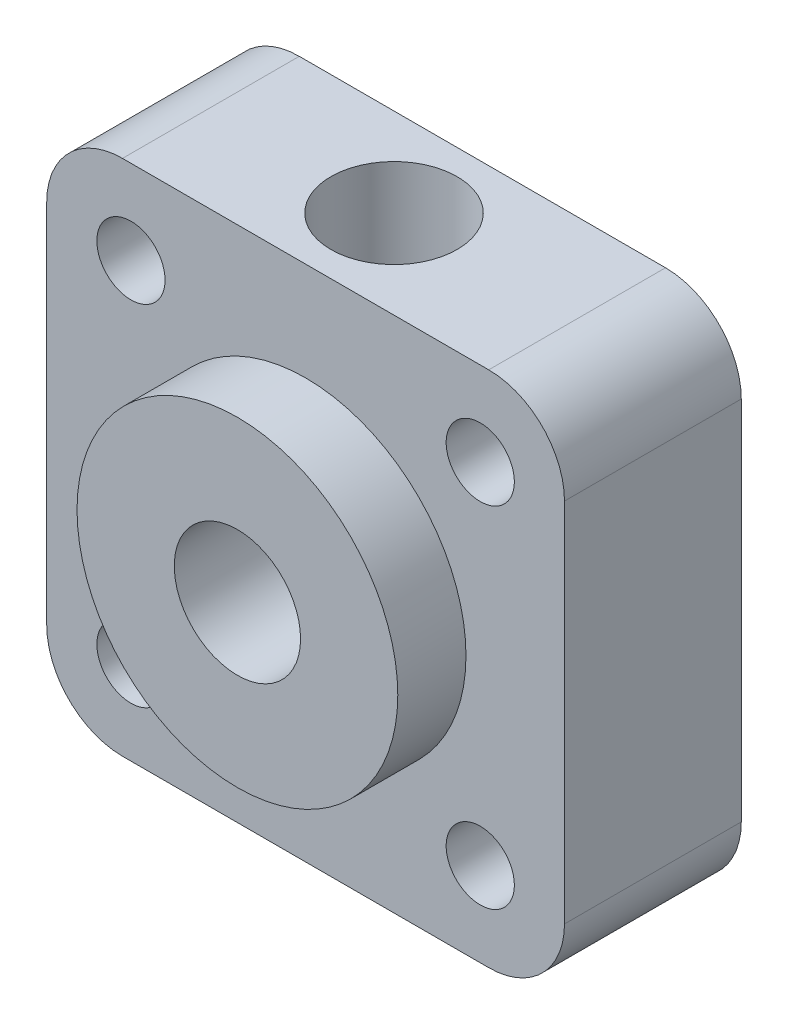
SolidWorks part; units mm, degrees
ref_plane "Alzado" through (0, 0, 0) normal (0, 0, 1) x (1, 0, 0)
ref_plane "Planta" through (0, 0, 0) normal (0, 1, 0) x (1, 0, 0)
ref_plane "Vista lateral" through (0, 0, 0) normal (1, 0, 0) x (0, 0, -1)
sketch "Croquis1" plane through (0, 0, 0) normal (0, 0, 1) x (1, 0, 0)
  line L1 (-10.25, 10.25) -> (10.25, 10.25)
  line L2 (-10.25, 10.25) -> (-10.25, -10.25)
  line L3 (-10.25, -10.25) -> (10.25, -10.25)
  line L4 (10.25, 10.25) -> (10.25, -10.25)
  line L5 (-10.25, 10.25) -> (10.25, -10.25) construction
  line L6 (-10.25, -10.25) -> (10.25, 10.25) construction
  point P0 (0, 0)
  dimension "D1" = 20.5
  dimension "D2" = 20.5
extrude "Saliente-Extruir1" add sketch "Croquis1" along normal blind 7
fillet "Redondeo1" radius 3 4 edges at (-10.25, -10.25, 3.5) (10.25, -10.25, 3.5) (10.25, 10.25, 3.5) (-10.25, 10.25, 3.5)
sketch "Croquis2" plane through (0, 0, 7) normal (0, 0, 1) x (1, 0, 0)
  circle A0 centre (0, 0) radius 6.35
  dimension "D1" = 12.7
extrude "Saliente-Extruir2" add sketch "Croquis2" along normal blind 2.7
sketch "Croquis3" plane through (0, 0, 9.7) normal (0, 0, 1) x (1, 0, 0)
  circle A0 centre (0, 0) radius 2.5
  dimension "D1" = 5
extrude "Cortar-Extruir1" cut sketch "Croquis3" against normal through all
sketch "Croquis4" plane through (0, 0, 7) normal (0, 0, 1) x (1, 0, 0)
  line L0 (-9.3713, 9.3713) -> (9.3713, -9.3713) construction
  line L1 (9.3713, 9.3713) -> (-9.3713, -9.3713) construction
  arc A0 (-7.25, 10.25) -> (-10.25, 7.25) centre (-7.25, 7.25) ccw construction
  arc A1 (7.25, -10.25) -> (10.25, -7.25) centre (7.25, -7.25) ccw construction
  arc A2 (10.25, 7.25) -> (7.25, 10.25) centre (7.25, 7.25) ccw construction
  arc A3 (-10.25, -7.25) -> (-7.25, -10.25) centre (-7.25, -7.25) ccw construction
  circle A4 centre (-6.9155, 6.9155) radius 1.35
  circle A5 centre (6.9155, 6.9155) radius 1.35
  circle A6 centre (6.9155, -6.9155) radius 1.35
  circle A7 centre (-6.9155, -6.9155) radius 1.35
  dimension "D1" = 2.7
  dimension "D2" = 2.7
  dimension "D3" = 2.7
  dimension "D4" = 2.7
  dimension "D5" = 9.78
  dimension "D6" = 9.78
  dimension "D7" = 9.78
  dimension "D8" = 9.78
extrude "Cortar-Extruir2" cut sketch "Croquis4" against normal through all
sketch "Croquis5" plane through (0, 10.25, 0) normal (0, 1, 0) x (1, 0, 0)
  line L0 (-7.25, 0) -> (7.25, -7) construction
  line L1 (-7.25, -7) -> (7.25, 0) construction
  circle A0 centre (0, -3.5) radius 2.5
  dimension "D1" = 5
extrude "Cortar-Extruir3" cut sketch "Croquis5" against normal up to next
